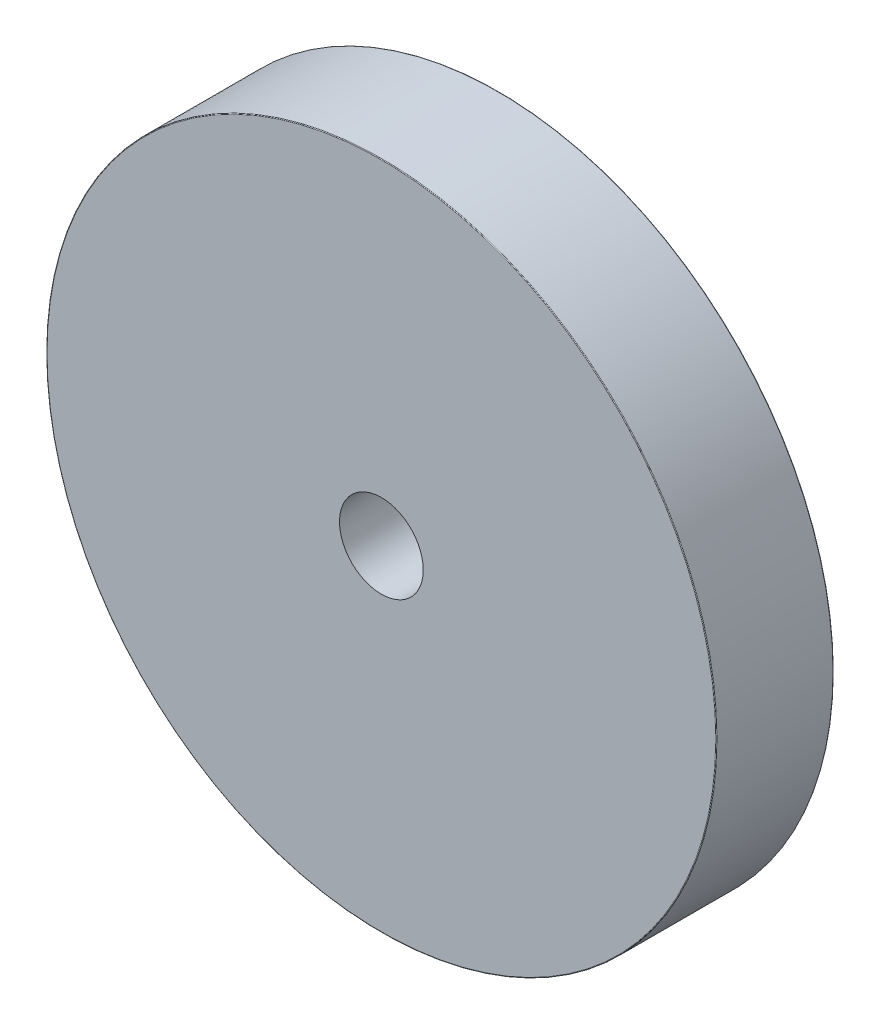
SolidWorks part; units mm, degrees
material "304 SSTL"
ref_plane "Front" through (0, 0, 0) normal (0, 0, 1) x (1, 0, 0)
ref_plane "Top" through (0, 0, 0) normal (0, 1, 0) x (1, 0, 0)
ref_plane "Right" through (0, 0, 0) normal (1, 0, 0) x (0, 0, -1)
sketch "Sketch1" plane through (0, 0, 0) normal (0, 0, 1) x (1, 0, 0)
  circle A0 centre (0, 0) radius 12.7
  circle A1 centre (0, 0) radius 1.5875
  dimension "D1" = 25.4
  dimension "D2" = 3.175
extrude "Extrude1" add sketch "Sketch1" along normal blind 4.445
fillet "Fillet1" radius 0.0254 2 edges at (12.7, 0, 0) (12.7, 0, 4.445)
